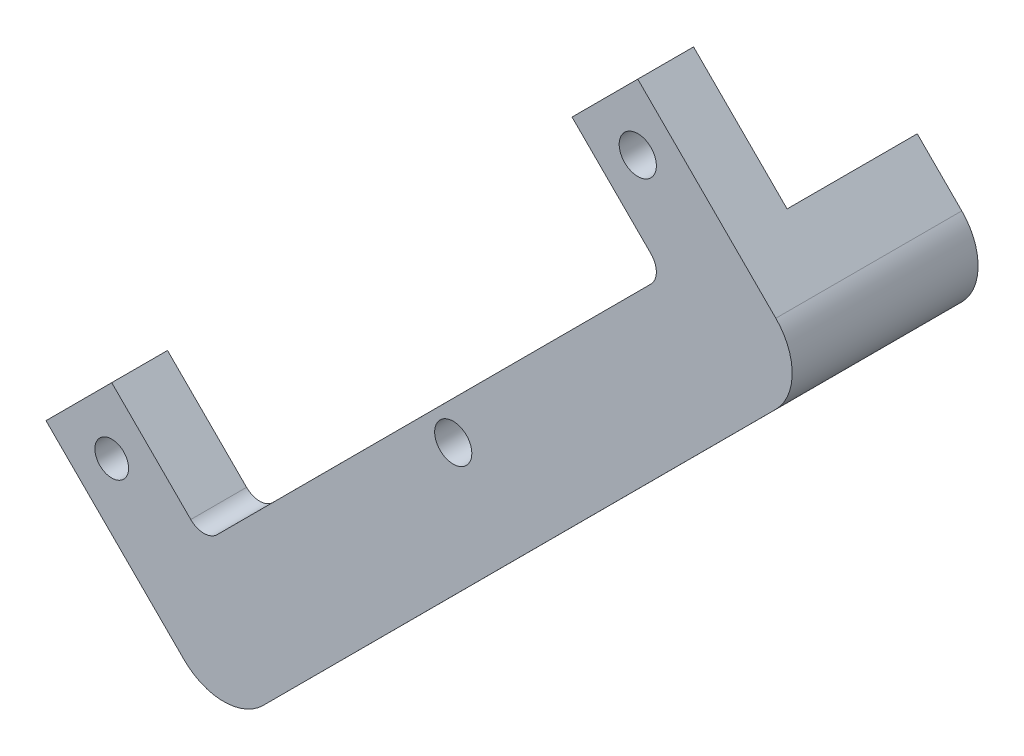
SolidWorks part; units mm, degrees
material "AISI 1018 Steel, Cold Rolled"
ref_plane "Front" through (0, 0, 0) normal (0, 0, 1) x (1, 0, 0)
ref_plane "Top" through (0, 0, 0) normal (0, 1, 0) x (1, 0, 0)
ref_plane "Right" through (0, 0, 0) normal (1, 0, 0) x (0, 0, -1)
sketch "Sketch1" plane through (0, 0, 0) normal (0, 0, 1) x (1, 0, 0)
  line L0 (-87.034, -176.6553) -> (-109.4769, -199.1137)
  line L2 (-109.4769, -199.1137) -> (-62.2707, -246.287)
  line L3 (23.025, -129.5306) -> (52.2142, -158.713) construction
  line L4 (70.1684, -19.5049) -> (97.1072, -46.4499)
  line L5 (92.616, 2.9488) -> (70.1684, -19.5049)
  line L6 (-87.034, -176.6553) -> (-60.0358, -203.6347)
  line L9 (97.1072, -55.429) -> (-51.0565, -203.6325)
  line L10 (92.616, 2.9488) -> (124.049, -28.4915)
  line L15 (124.049, -28.4915) -> (139.7616, -44.2077)
  line L16 (139.7616, -71.1453) -> (-35.3331, -246.2807)
  arc A0 (97.1072, -55.429) -> (97.1072, -46.4499) centre (92.6165, -50.9395) ccw
  circle A1 centre (29.5915, -136.0913) radius 6.35
  arc A2 (139.7616, -71.1453) -> (139.7616, -44.2077) centre (126.2896, -57.6765) ccw
  arc A3 (-51.0565, -203.6325) -> (-60.0358, -203.6347) centre (-55.5473, -199.143) cw
  arc A4 (-35.3331, -246.2807) -> (-62.2707, -246.287) centre (-48.805, -232.8119) cw
  dimension "D4" = 44.45
  dimension "D5" = 285.75
  dimension "D3" = 19.05
  dimension "D2" = 6.35
  dimension "D7" = 142.875
  dimension "D6" = 6.35
  dimension "D8" = 31.75
  dimension "D1" = 31.75
extrude "Base-Extrude" add sketch "Sketch1" along normal blind 63.5
sketch "Sketch2" plane through (-154.2571, -154.3647, 0) normal (-0.7069, -0.7074, 0) x (0.7074, -0.7069, 0)
  line L0 (63.3067, 63.5) -> (63.3067, 0) construction
  line L1 (63.3067, 0) -> (108.6084, 0)
  line L2 (63.3067, 0) -> (130.043, 0) construction
  line L3 (149.093, 63.5) -> (149.093, 0) construction
  line L6 (108.6084, 44.45) -> (108.6084, 0)
  line L7 (63.3067, 44.45) -> (108.6084, 44.45)
  line L9 (63.3067, 44.45) -> (63.3067, 0)
  dimension "D2" = 40.4846
  dimension "D1" = 44.45
extrude "Cut-Extrude1" cut sketch "Sketch2" against normal through all
hole_wizard "1/2-20 Tapped Hole4" positions "Sketch4" profile "Sketch3" tap size "1/2-20" standard "Ansi Inch" end condition through all
sketch "Sketch4" plane through (0, 0, 63.5) normal (0, 0, 1) x (1, 0, 0)
  line L2 (-87.034, -176.6553) -> (-109.4769, -199.1137) construction
  line L3 (-109.4769, -199.1137) -> (-62.2707, -246.287) construction
  point P0 (-87.0262, -199.1059)
  dimension "D1" = 15.875
  dimension "D2" = 15.875
sketch "Sketch3" plane through (-87.0262, -199.1059, 63.5) normal (1, 0, 0) x (0, -1, 0)
  line L0 (0, 0) -> (0, 63.5)
  line L1 (0, 63.5) -> (5.7544, 63.5)
  line L2 (5.7544, 63.5) -> (5.7544, 0)
  line L5 (5.7544, 0) -> (0, 0)
  line L11 (0, -6.35) -> (0, 107.95) construction
  dimension "Thru Tap Drill Dia." = 11.5087
  dimension "Thru Tap Drill Depth" = 63.5
cosmetic thread "Cosmetic Thread2" parameters "D1"=19.05, "D2"=12.7
hole_wizard "1/2-20 Tapped Hole3" positions "Sketch6" profile "Sketch5" tap size "1/2-20" standard "Ansi Inch" end condition through all
sketch "Sketch6" plane through (0, 0, 63.5) normal (0, 0, 1) x (1, 0, 0)
  line L0 (92.616, 2.9488) -> (70.1684, -19.5049) construction
  line L1 (139.7616, -44.2077) -> (92.616, 2.9488) construction
  point P0 (92.6162, -19.5047)
  dimension "D1" = 15.875
  dimension "D2" = 15.875
sketch "Sketch5" plane through (92.6162, -19.5047, 63.5) normal (1, 0, 0) x (0, -1, 0)
  line L0 (0, 0) -> (0, 63.5)
  line L1 (0, 63.5) -> (5.7544, 63.5)
  line L3 (5.7544, 63.5) -> (5.7544, 25.4)
  line L4 (5.7544, 25.4) -> (6.35, 25.4)
  line L5 (6.35, 25.4) -> (6.35, 0)
  line L7 (6.35, 0) -> (0, 0)
  line L11 (0, -6.35) -> (0, 107.95) construction
  dimension "Thru Tap Drill Dia." = 11.5087
  dimension "Thru Tap Drill Depth" = 63.5
  dimension "Thread Dia." = 12.7
  dimension "Thread Depth" = 25.4
hole_wizard "1/2-20 Tapped Hole1" positions "Sketch8" profile "Sketch7" tap size "1/2-20" standard "Ansi Inch" end condition through all
sketch "Sketch8" plane through (105.4697, -105.4452, 0) normal (0.7072, -0.707, 0) x (0, 0, -1)
  line L0 (0, -199.1483) -> (0, 48.5017) construction
  line L1 (-63.5, 67.5517) -> (0, 67.5517) construction
  point P0 (-25.4, 16.7517)
  dimension "D1" = 25.4
  dimension "D2" = 50.8
sketch "Sketch7" plane through (117.3135, -93.5986, 25.4) normal (0, 0, 1) x (0.707, 0.7072, 0)
  line L0 (0, 0) -> (0, 228.645)
  line L1 (0, 228.645) -> (6.35, 228.645)
  line L2 (6.35, 228.645) -> (6.35, 0)
  line L5 (6.35, 0) -> (0, 0)
  line L11 (0, -6.35) -> (0, 107.95) construction
  dimension "Thread Major Dia." = 12.7
  dimension "Thru Tap Drill Depth" = 228.645
hole_wizard "1/2-20 Tapped Hole2" positions "Sketch10" profile "Sketch9" tap size "1/2-20" standard "Ansi Inch" end condition through all
sketch "Sketch10" plane through (105.4697, -105.4452, 0) normal (0.7072, -0.707, 0) x (0, 0, -1)
  line L0 (0, -199.1483) -> (0, 48.5017) construction
  line L1 (-63.5, -218.1983) -> (0, -218.1983) construction
  point P0 (-25.4, -167.3983)
  dimension "D1" = 25.4
  dimension "D2" = 50.8
sketch "Sketch9" plane through (-12.885, -223.8274, 25.4) normal (0, 0, 1) x (0.707, 0.7072, 0)
  line L0 (0, 0) -> (0, 228.645)
  line L1 (0, 228.645) -> (5.7544, 228.645)
  line L2 (5.7544, 228.645) -> (5.7544, 0)
  line L5 (5.7544, 0) -> (0, 0)
  line L11 (0, -6.35) -> (0, 107.95) construction
  dimension "Thru Tap Drill Dia." = 11.5087
  dimension "Thru Tap Drill Depth" = 228.645
cosmetic thread "Cosmetic Thread1" parameters "D2"=12.7
